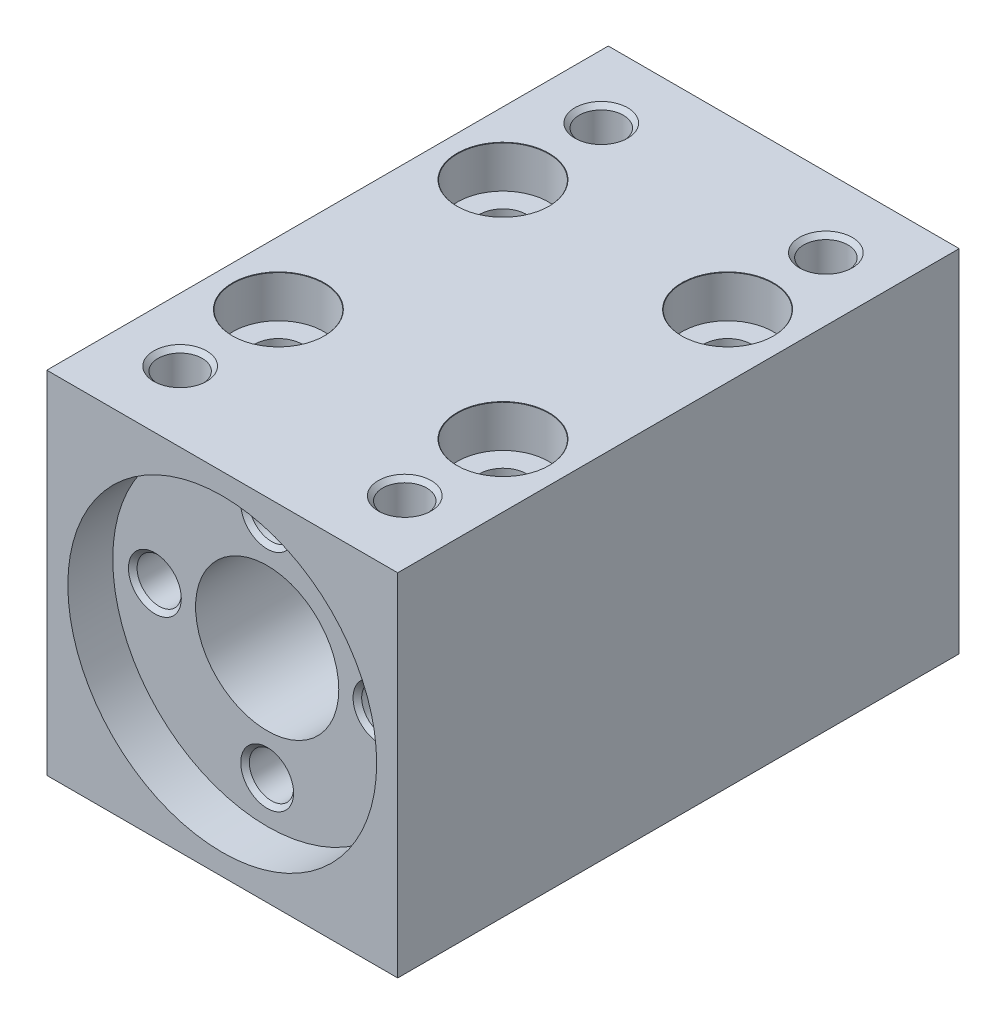
SolidWorks part; units mm, degrees
material "Liga 6061"
ref_plane "Plano frontal" through (0, 0, 0) normal (0, 0, 1) x (1, 0, 0)
ref_plane "Plano superior" through (0, 0, 0) normal (0, 1, 0) x (1, 0, 0)
ref_plane "Plano direito" through (0, 0, 0) normal (1, 0, 0) x (0, 0, -1)
sketch "Esboço1" plane through (0, 0, 0) normal (0, 0, 1) x (1, 0, 0)
  line L1 (12.5, -12.5) -> (-12.5, -12.5)
  line L2 (12.5, -12.5) -> (12.5, 12.5)
  line L3 (12.5, 12.5) -> (-12.5, 12.5)
  line L4 (-12.5, -12.5) -> (-12.5, 12.5)
  line L5 (12.5, -12.5) -> (-12.5, 12.5) construction
  line L6 (12.5, 12.5) -> (-12.5, -12.5) construction
  point P0 (0, 0)
  dimension "D1" = 25
  dimension "D2" = 25
extrude "Ressalto-extrusão1" add sketch "Esboço1" along normal blind 40
sketch "Esboço2" plane through (0, 0, 40) normal (0, 0, 1) x (1, 0, 0)
  line L0 (0, -13.6719) -> (0, 16.5889) construction
  circle A0 centre (0, 0) radius 5.1
  dimension "D1" = 10.2
extrude "Corte-extrusão1" cut sketch "Esboço2" against normal through all
sketch "Esboço3" plane through (0, 0, 40) normal (0, 0, 1) x (1, 0, 0)
  circle A0 centre (0, 0) radius 11
  dimension "D1" = 22
extrude "Corte-extrusão2" cut sketch "Esboço3" against normal blind 3.2
hole_wizard "Furo roscado para conduíte de M3x0.52" positions "Esboço9" profile "Esboço10" tap size "M3x0.5" standard "Helicoil® Metric"
sketch "Esboço9" plane through (0, 0, 36.8) normal (0, 0, 1) x (1, 0, 0)
  point P0 (0, 8)
  point P8 (8, 0)
  point P9 (0, -8)
  point P10 (-8, 0)
  dimension "D1" = 8
  dimension "D2" = 4
sketch "Esboço10" plane through (0, 8, 36.8) normal (1, 0, 0) x (0, -1, 0)
  line L0 (0, 0) -> (0, 6.9464)
  line L1 (0, 6.9464) -> (1.575, 6)
  line L2 (1.575, 6) -> (1.575, 0.308)
  line L3 (1.575, 0.308) -> (1.883, 0)
  line L5 (1.883, 0) -> (0, 0)
  line L6 (-1.575, 0.308) -> (-1.883, 0) construction
  line L10 (0, 6.9464) -> (-1.575, 6) construction
  line L11 (0, -6.35) -> (0, 107.95) construction
  dimension "Tap Drill Dia." = 3.15
  dimension "Tap Drill Depth" = 6
  dimension "Near C'Sink Dia." = 3.766
  dimension "Near C'Sink Angle" = 90
  dimension "Drill Angle" = 118
cosmetic thread "Rosca de furo5" parameters "D1"=3.5, "D2"=3.716
cosmetic thread "Rosca de furo6" parameters "D1"=3.5, "D2"=3.716
cosmetic thread "Rosca de furo7" parameters "D1"=3.5, "D2"=3.716
cosmetic thread "Rosca de furo8" parameters "D1"=3.5, "D2"=3.716
hole_wizard "Rebaixo para SHCS M31" positions "Esboço11" profile "Esboço13" counterbore size "M3" standard "Ansi Metric" end condition through all
sketch "Esboço11" plane through (0, 12.5, 0) normal (0, 1, 0) x (1, 0, 0)
  line L0 (0, 4.0189) -> (0, -45.0632) construction
  line L2 (14.6898, -20) -> (-19.424, -20) construction
  point P0 (-8, -12)
  point P2 (8, -12)
  point P4 (-8, -28)
  point P6 (8, -28)
  dimension "D1" = 8
  dimension "D2" = 8
  dimension "D3" = 8
  dimension "D4" = 8
  dimension "D5" = 8
  dimension "D6" = 8
  dimension "D7" = 8
  dimension "D8" = 8
sketch "Esboço13" plane through (-8, 12.5, 12) normal (1, 0, 0) x (0, 0, 1)
  line L0 (0, 0) -> (0, 25)
  line L1 (0, 25) -> (1.7, 25)
  line L3 (1.7, 25) -> (1.7, 3)
  line L4 (3.25, 3) -> (1.7, 3)
  line L5 (3.25, 3) -> (3.25, 0.025)
  line L6 (3.25, 0.025) -> (3.275, 0)
  line L7 (3.275, 0) -> (0, 0)
  line L8 (-3.25, 0.025) -> (-3.275, 0) construction
  line L11 (0, -6.35) -> (0, 107.95) construction
  dimension "Thru Hole Dia." = 3.4
  dimension "Thru Hole Depth" = 25
  dimension "C'Bore Dia." = 6.5
  dimension "C'Bore Depth" = 3
  dimension "Near C'Sink Dia." = 6.55
  dimension "Near C'Sink Angle" = 90
hole_wizard "Furo roscado para conduíte de M3x0.53" positions "Esboço15" profile "Esboço16" tap size "M3x0.5" standard "Helicoil® Metric"
sketch "Esboço15" plane through (0, 12.5, 0) normal (0, 1, 0) x (1, 0, 0)
  line L0 (0, 4.1582) -> (0, -42.2088) construction
  line L2 (16.5696, -19.0253) -> (-17.1962, -19.0253) construction
  line L4 (12.5, 0) -> (-12.5, 0) construction
  line L5 (12.5, -40) -> (-12.5, -40) construction
  point P0 (-8, -5)
  point P2 (8, -5)
  point P4 (-8, -35)
  point P6 (8, -35)
  dimension "D1" = 8
  dimension "D2" = 5
  dimension "D3" = 8
  dimension "D4" = 5
  dimension "D5" = 8
  dimension "D6" = 5
  dimension "D7" = 5
  dimension "D8" = 8
sketch "Esboço16" plane through (-8, 12.5, 5) normal (1, 0, 0) x (0, 0, 1)
  line L0 (0, 0) -> (0, 8.9464)
  line L1 (0, 8.9464) -> (1.575, 8)
  line L2 (1.575, 8) -> (1.575, 0.308)
  line L3 (1.575, 0.308) -> (1.883, 0)
  line L5 (1.883, 0) -> (0, 0)
  line L6 (-1.575, 0.308) -> (-1.883, 0) construction
  line L10 (0, 8.9464) -> (-1.575, 8) construction
  line L11 (0, -6.35) -> (0, 107.95) construction
  dimension "Tap Drill Dia." = 3.15
  dimension "Tap Drill Depth" = 8
  dimension "Near C'Sink Dia." = 3.766
  dimension "Near C'Sink Angle" = 90
  dimension "Drill Angle" = 118
cosmetic thread "Rosca de furo9" parameters "D1"=3.5, "D2"=3.716
cosmetic thread "Rosca de furo10" parameters "D1"=3.5, "D2"=3.716
cosmetic thread "Rosca de furo11" parameters "D1"=3.5, "D2"=3.716
cosmetic thread "Rosca de furo12" parameters "D1"=3.5, "D2"=3.716
